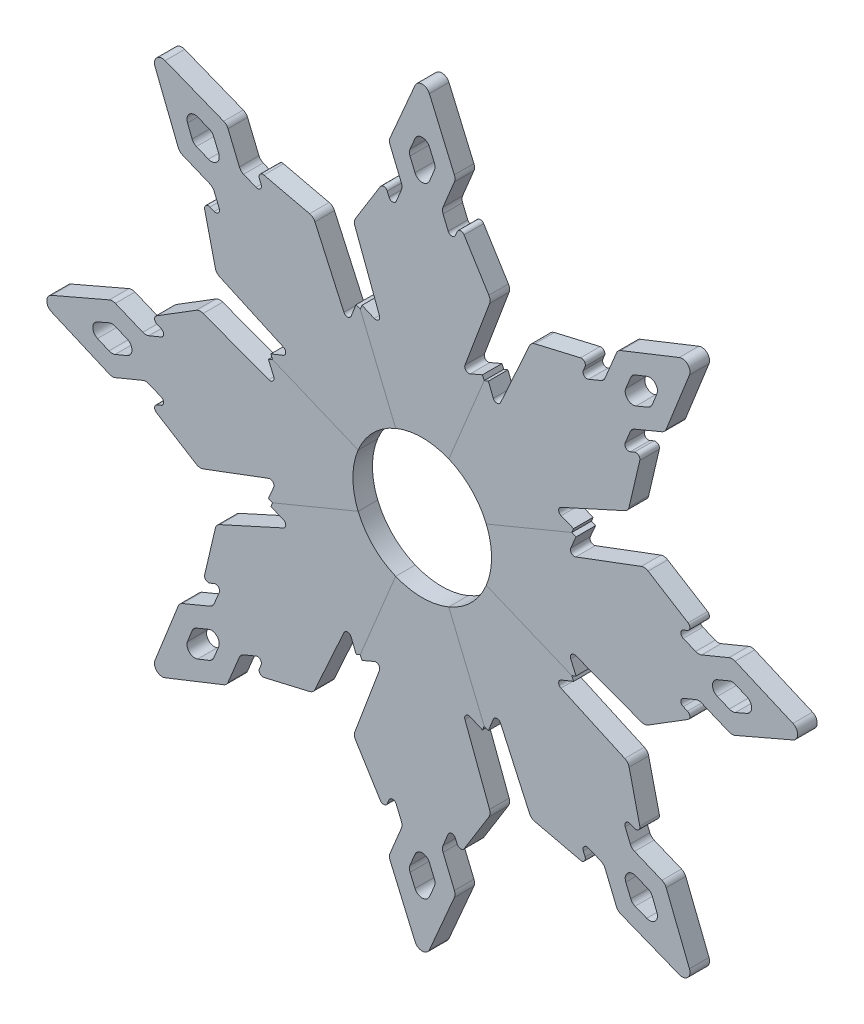
SolidWorks part; units mm, degrees
other "Markup1"
sketch "Sketch2" plane through (-101.7437, -116.8741, 5) normal (0, 0, 1) x (1, 0, 0)
other "Markup2"
sketch "Sketch3" plane through (-97.2054, -110.6569, 5) normal (0, 0, 1) x (1, 0, 0)
material "Листовой ламинированный компаунд"
ref_plane "Front" through (0, 0, 0) normal (0, 0, 1) x (1, 0, 0)
ref_plane "Top" through (0, 0, 0) normal (0, 1, 0) x (1, 0, 0)
ref_plane "Right" through (0, 0, 0) normal (1, 0, 0) x (0, 0, -1)
sketch "Эскиз1" plane through (0, 0, 0) normal (0, 0, 1) x (1, 0, 0)
  line L0 (-8.0348, 1.6697) -> (-17.0965, 23.5464)
  line L1 (-17.0965, 23.5464) -> (-16.6406, 24.6028)
  line L2 (-16.6406, 24.6028) -> (-13.5095, 23.2515)
  line L3 (-12.1769, 24.5208) -> (-18.4609, 41.278)
  line L4 (-18.2872, 43.0355) -> (-11.9558, 53.2293)
  line L5 (-10.1824, 53.0844) -> (-9.7371, 52.0092)
  line L6 (-7.8893, 52.0092) -> (-6.5774, 55.1765)
  line L7 (-6.5774, 56.7072) -> (-9.4772, 63.708)
  line L8 (-9.4657, 65.2658) -> (-3.0889, 80.0412)
  line L9 (-1.2526, 84.2959) -> (-1.2526, -17.2198) construction
  line L10 (-3.0889, 68.2797) -> (-4.3576, 65.34)
  line L11 (-4.3691, 63.7821) -> (-3.1004, 60.7191)
  line L12 (1.8639, 63.7821) -> (0.5952, 60.7191)
  line L13 (0.5837, 68.2797) -> (1.8524, 65.34)
  line L14 (6.9605, 65.2658) -> (0.5837, 80.0412)
  line L15 (4.0722, 56.7072) -> (6.972, 63.708)
  line L16 (5.3841, 52.0092) -> (4.0722, 55.1765)
  line L17 (7.6772, 53.0844) -> (7.2319, 52.0092)
  line L18 (15.782, 43.0355) -> (9.4506, 53.2293)
  line L19 (9.6717, 24.5208) -> (15.9557, 41.278)
  line L20 (14.1354, 24.6028) -> (11.0043, 23.2515)
  line L21 (14.5913, 23.5464) -> (14.1354, 24.6028)
  line L22 (5.5296, 1.6697) -> (14.5913, 23.5464)
  arc A0 (5.5296, 1.6697) -> (-8.0348, 1.6697) centre (-1.2526, -14.7041) ccw
  arc A1 (15.782, 43.0355) -> (15.9557, 41.278) centre (14.083, 41.9803) cw
  arc A2 (-18.4609, 41.278) -> (-18.2872, 43.0355) centre (-16.5882, 41.9803) cw
  arc A3 (4.0722, 56.7072) -> (4.0722, 55.1765) centre (5.9199, 55.9419) ccw
  arc A4 (-6.5774, 55.1765) -> (-6.5774, 56.7072) centre (-8.4251, 55.9419) ccw
  arc A5 (6.9605, 65.2658) -> (6.972, 63.708) centre (5.1242, 64.4733) cw
  arc A6 (-9.4772, 63.708) -> (-9.4657, 65.2658) centre (-7.6294, 64.4733) cw
  arc A7 (1.8639, 63.7821) -> (1.8524, 65.34) centre (0.0161, 64.5475) ccw
  arc A8 (-4.3576, 65.34) -> (-4.3691, 63.7821) centre (-2.5213, 64.5475) ccw
  arc A9 (-3.1004, 60.7191) -> (0.5952, 60.7191) centre (-1.2526, 61.4845) ccw
  arc A10 (-3.0889, 80.0412) -> (0.5837, 80.0412) centre (-1.2526, 79.2486) cw
  arc A11 (-3.0889, 68.2797) -> (0.5837, 68.2797) centre (-1.2526, 67.4872) cw
  arc A12 (9.6717, 24.5208) -> (11.0043, 23.2515) centre (10.608, 24.1696) ccw
  arc A13 (-13.5095, 23.2515) -> (-12.1769, 24.5208) centre (-13.1133, 24.1696) ccw
  arc A14 (7.6772, 53.0844) -> (9.4506, 53.2293) centre (8.6011, 52.7017) cw
  arc A15 (5.3841, 52.0092) -> (7.2319, 52.0092) centre (6.308, 52.3919) ccw
  arc A16 (-11.9558, 53.2293) -> (-10.1824, 53.0844) centre (-11.1063, 52.7017) cw
  arc A17 (-9.7371, 52.0092) -> (-7.8893, 52.0092) centre (-8.8132, 52.3919) ccw
  point P27 (-1.2526, -14.7041)
  point P28 (16.3012, 42.1995)
  point P31 (-18.8065, 42.1995)
  point P34 (3.7551, 55.9419)
  point P37 (-6.2604, 55.9419)
  point P40 (7.2956, 64.4893)
  point P43 (-9.8008, 64.4893)
  point P46 (2.1875, 64.5635)
  point P49 (-4.6927, 64.5635)
  point P52 (-1.2526, 56.2582)
  point P58 (-1.2526, 72.5344)
  point P61 (8.8465, 22.3202)
  point P64 (-11.3517, 22.3202)
  point P67 (8.4227, 54.8842)
  point P70 (6.308, 49.7788)
  point P73 (-10.9279, 54.8842)
  point P76 (-8.8132, 49.7788)
  point P77 (-1.2526, -17.2198)
  dimension "D1" = 45
  dimension "D3" = 2
  dimension "D4" = 1
  dimension "D2" = 99
extrude "Бобышка-Вытянуть1" add sketch "Эскиз1" along normal blind 5
pattern_circular "CirPattern1" count 8 over 360 about axis through (-1.2526, -14.7041, 0) along (0, 0, 1) of bodies 101
